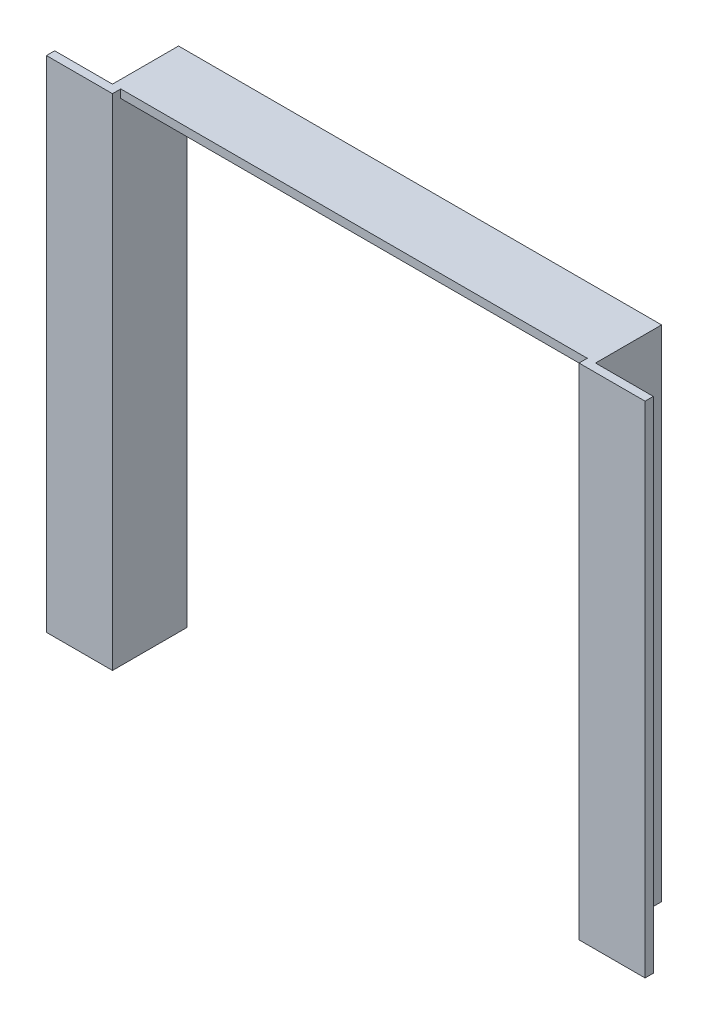
SolidWorks part; units mm, degrees
ref_plane "Front Plane" through (0, 0, 0) normal (0, 0, 1) x (1, 0, 0)
ref_plane "Top Plane" through (0, 0, 0) normal (0, 1, 0) x (1, 0, 0)
ref_plane "Right Plane" through (0, 0, 0) normal (1, 0, 0) x (0, 0, -1)
sketch "Sketch1" plane through (0, 0, 0) normal (0, 0, 1) x (1, 0, 0)
  line L0 (0, 0) -> (0, 188.9125)
  line L1 (0, 188.9125) -> (179.3875, 188.9125)
  line L2 (179.3875, 188.9125) -> (179.3875, 0)
  line L3 (179.3875, 0) -> (182.5625, 0)
  line L4 (182.5625, 0) -> (182.5625, 192.0875)
  line L5 (182.5625, 192.0875) -> (-3.175, 192.0875)
  line L6 (-3.175, 192.0875) -> (-3.175, 0)
  line L7 (-3.175, 0) -> (0, 0)
  dimension "D1" = 3.175
  dimension "D2" = 3.175
  dimension "D3" = 3.175
  dimension "D4" = 185.7375
  dimension "D5" = 188.9125
extrude "Boss-Extrude1" add sketch "Sketch1" along normal mid plane 25.4
sketch "Sketch2" plane through (0, 0, 0) normal (1, 0, 0) x (0, 0, -1)
  line L0 (-12.7, 192.0875) -> (-12.7, 0) construction
  line L1 (-12.7, 0) -> (-15.875, 0)
  line L2 (-12.7, 0) -> (-12.7, 192.0875)
  line L3 (-12.7, 192.0875) -> (-15.875, 192.0875)
  line L4 (-15.875, 0) -> (-15.875, 192.0875)
  line L6 (-12.7, 192.0875) -> (12.7, 192.0875) construction
  dimension "D1" = 3.175
extrude "Boss-Extrude2" add sketch "Sketch2" against normal blind 25.4
ref_plane "Plane1" through (89.6937, 0, 0) normal (1, 0, 0) x (0, 0, -1)
mirror "Mirror1" about plane through (89.6937, 0, 0) normal (1, 0, 0) of "Boss-Extrude2"
